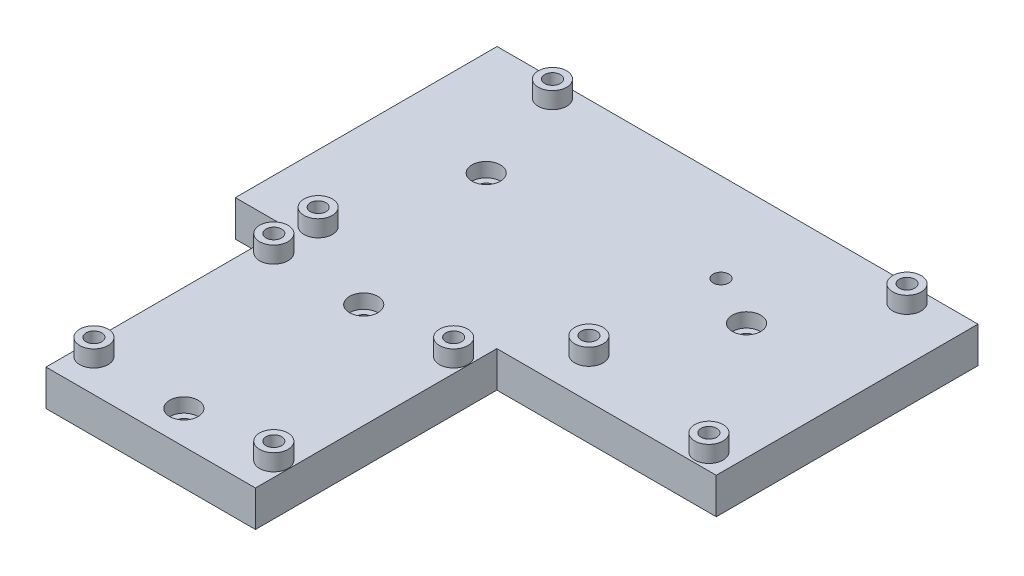
SolidWorks part; units mm, degrees
ref_plane "Front Plane" through (0, 0, 0) normal (0, 0, 1) x (1, 0, 0)
ref_plane "Top Plane" through (0, 0, 0) normal (0, 1, 0) x (1, 0, 0)
ref_plane "Right Plane" through (0, 0, 0) normal (1, 0, 0) x (0, 0, -1)
sketch "Sketch1" plane through (0, 0, 0) normal (0, 1, 0) x (1, 0, 0)
  line L0 (44.25, 52) -> (90.6, 52)
  line L1 (0, 0) -> (44.25, 0)
  line L4 (44.25, 0) -> (44.25, 52)
  line L5 (-11, 105.3) -> (90.6, 105.3)
  line L6 (90.6, 105.3) -> (90.6, 52)
  line L7 (0, 0) -> (0, 52)
  line L8 (0, 52) -> (-11, 52)
  line L9 (-11, 52) -> (-11, 105.3)
  line L10 (3.125, 45) -> (3.125, 7) construction
  line L11 (3.125, 7) -> (41.125, 7) construction
  line L12 (41.125, 7) -> (41.125, 45) construction
  line L13 (41.125, 45) -> (3.125, 45) construction
  line L14 (90.6, 52) -> (90.6, 51)
  line L15 (90.6, 51) -> (44.25, 51)
  line L16 (-11, 52) -> (-11, 51)
  line L17 (-11, 51) -> (0, 51)
  line L18 (-11, 105.3) -> (-11, 106.3)
  line L19 (-11, 106.3) -> (90.6, 106.3)
  line L20 (90.6, 106.3) -> (90.6, 105.3)
  circle A0 centre (4.3, 102.7) radius 1.65
  circle A1 centre (79.2, 102.7) radius 1.65
  circle A2 centre (3, 54.5) radius 1.65
  circle A3 centre (55.1, 87.5) radius 1.65
  circle A4 centre (55.1, 59.6) radius 1.65
  circle A5 centre (85.55, 54.5) radius 1.65
  circle A7 centre (3.125, 45) radius 1.65
  circle A8 centre (41.125, 45) radius 1.65
  circle A10 centre (3.125, 7) radius 1.65
  circle A11 centre (41.125, 7) radius 1.65
  circle A12 centre (11, 82) radius 1.65
  circle A13 centre (66, 82) radius 1.65
  circle A14 centre (22.125, 45) radius 1.65
  circle A15 centre (22.125, 7) radius 1.65
  point P25 (22.125, 7)
  point P26 (22.125, 0)
  point P27 (3.125, 26)
  point P28 (0, 26)
  dimension "D3" = 74.9
  dimension "D4" = 15.3
  dimension "D5" = 3.3
  dimension "D6" = 14
  dimension "D7" = 2.5
  dimension "D8" = 66.1
  dimension "D9" = 7.6
  dimension "D12" = 50.7
  dimension "D17" = 3.3
  dimension "D19" = 55
  dimension "D20" = 21.75
  dimension "D21" = 30
  dimension "D22" = 82.55
  dimension "D23" = 1
  dimension "D1" = 52
  dimension "D2" = 44.25
  dimension "D10" = 35.5
  dimension "D11" = 53.3
  dimension "D13" = 101.6
  dimension "D14" = 38
  dimension "D15" = 38
  dimension "D16" = 52
  dimension "D18" = 11
  dimension "D24" = 1
  dimension "D25" = 1
extrude "Boss-Extrude1" add sketch "Sketch1" along normal blind 7.6 contours L16 L17 L7 L8 | L20 L19 L18 L5 | L15 L14 L0 L4 | L9 L8 L7 L1 L4 L0 L6 L5 A15 A14 A13 A12 A11 A10 A8 A7 A5 A4 A3 A2 A1 A0
sketch "Sketch2" plane through (0, 7.6, 0) normal (0, 1, 0) x (1, 0, 0)
  circle A0 centre (11, 82) radius 3
  circle A1 centre (66, 82) radius 3
  circle A2 centre (22.125, 45) radius 3
  circle A3 centre (22.125, 7) radius 3
  dimension "D1" = 6
extrude "Cut-Extrude1" cut sketch "Sketch2" against normal blind 3
sketch "Sketch3" plane through (0, 7.6, 0) normal (0, 1, 0) x (1, 0, 0)
  circle A0 centre (3.125, 7) radius 3
  circle A1 centre (41.125, 7) radius 3
  circle A2 centre (3.125, 45) radius 3
  circle A3 centre (41.125, 45) radius 3
  circle A4 centre (3, 54.5) radius 3
  circle A5 centre (55.1, 59.6) radius 3
  circle A6 centre (85.55, 54.5) radius 3
  circle A7 centre (79.2, 102.7) radius 3
  circle A8 centre (4.3, 102.7) radius 3
  circle A9 centre (3.125, 7) radius 1.65
  circle A10 centre (41.125, 7) radius 1.65
  circle A11 centre (41.125, 45) radius 1.65
  circle A12 centre (3.125, 45) radius 1.65
  circle A13 centre (3, 54.5) radius 1.65
  circle A14 centre (85.55, 54.5) radius 1.65
  circle A16 centre (55.1, 59.6) radius 1.65
  circle A17 centre (4.3, 102.7) radius 1.65
  circle A18 centre (79.2, 102.7) radius 1.65
  dimension "D1" = 6
extrude "Boss-Extrude3" add sketch "Sketch3" along normal blind 3.5
